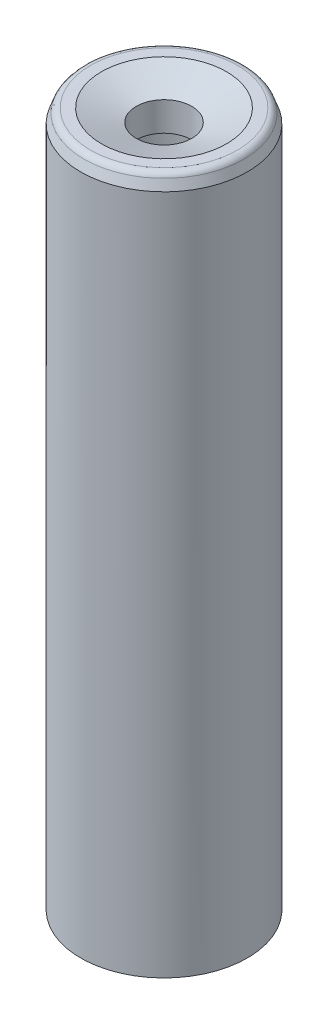
SolidWorks part; units mm, degrees
ref_plane "Alzado" through (0, 0, 0) normal (0, 0, 1) x (1, 0, 0)
ref_plane "Planta" through (0, 0, 0) normal (0, 1, 0) x (1, 0, 0)
ref_plane "Vista lateral" through (0, 0, 0) normal (1, 0, 0) x (0, 0, -1)
sketch "Croquis1" plane through (0, 0, 0) normal (0, 1, 0) x (1, 0, 0)
  circle A0 centre (0, 0) radius 4
  circle A1 centre (0, 0) radius 6
extrude "Saliente-Extruir1" add sketch "Croquis1" along normal blind 40
ref_plane "Plano1" through (0, 37, 0) normal (0, 1, 0) x (1, 0, 0)
sketch "Croquis2" plane through (0, 37, 0) normal (0, 1, 0) x (1, 0, 0)
  circle A0 centre (0, 0) radius 4 construction
  circle A1 centre (0, 0) radius 4
extrude "Saliente-Extruir2" add sketch "Croquis2" along normal up to surface (3 mm away) up to face at (0, 40, 6)
sketch "Croquis3" plane through (0, 40, 0) normal (0, 1, 0) x (1, 0, 0)
  circle A0 centre (0, 0) radius 2
extrude "Cortar-Extruir1" cut sketch "Croquis3" against normal blind 40
chamfer "Chaflán1" distance 2.5 angle 20 1 edges at (0, 40, 2)
chamfer "Chaflán2" distance 1 angle 20 1 edges at (0, 40, 6)
fillet "Redondeo1" radius 0.5 1 edges at (0, 40, 5.636)
sketch "Croquis4" plane through (0, 0, 0) normal (0, -1, 0) x (1, 0, 0)
  circle A0 centre (0, 0) radius 4 construction
  circle A1 centre (0, 0) radius 6
  circle A2 centre (0, 0) radius 6
  circle A3 centre (0, 0) radius 4
  dimension "D1" = 0
extrude "Saliente-Extruir3" add sketch "Croquis4" along normal blind 10
